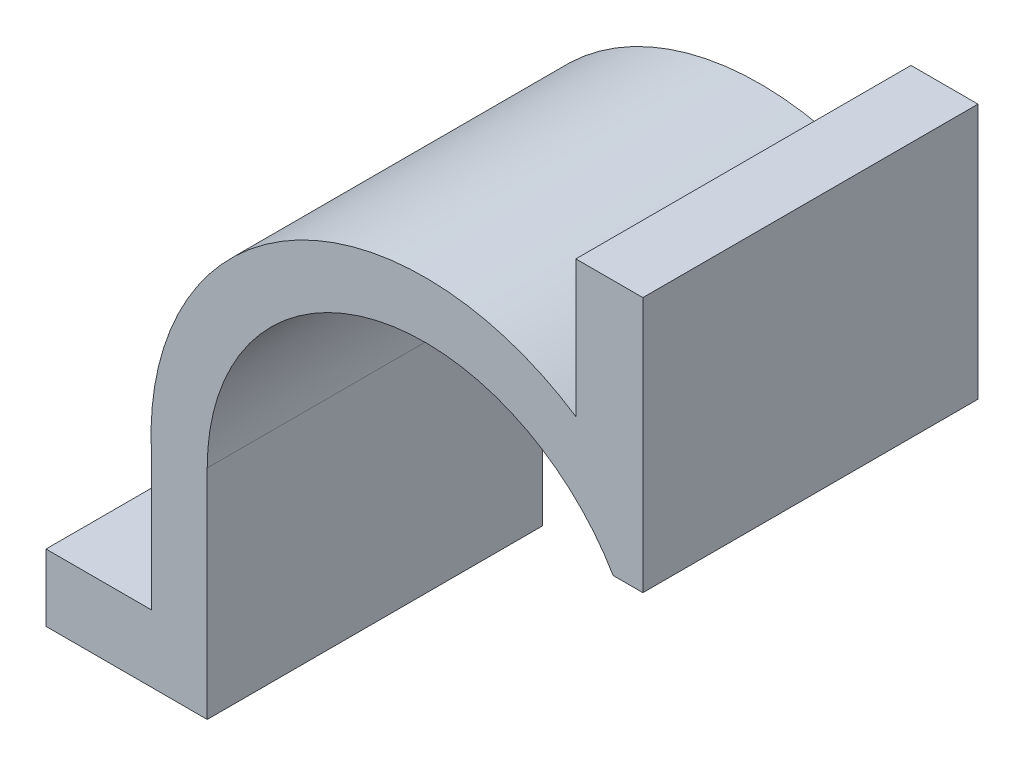
SolidWorks part; units mm, degrees
ref_plane "Front Plane" through (0, 0, 0) normal (0, 0, 1) x (1, 0, 0)
ref_plane "Top Plane" through (0, 0, 0) normal (0, 1, 0) x (1, 0, 0)
ref_plane "Right Plane" through (0, 0, 0) normal (1, 0, 0) x (0, 0, -1)
sketch "Sketch2" plane through (0, 0, 0) normal (0, 0, 1) x (1, 0, 0)
  line L0 (32.5, 0) -> (0, 0) construction
  line L1 (32.5, 0) -> (32.5, 54.5133) construction
  line L2 (43.1161, -32.5) -> (-56.5532, -32.5) construction
  line L3 (0, 32.5) -> (39.8302, 32.5) construction
  line L4 (-32.5, 0) -> (-32.5, -32.5)
  line L5 (-32.5, -31.4301) -> (-32.5, 0) construction
  line L6 (-32.5, -32.5) -> (-56.5532, -32.5)
  line L7 (-56.5532, -32.5) -> (-56.5532, -22.5)
  line L8 (-56.5532, -22.5) -> (-40.8374, -22.5)
  line L9 (-40.8374, -22.5) -> (-40.8374, -2.0108)
  line L10 (28.0694, 16.3817) -> (32.5, 16.3817)
  line L11 (32.5, 16.3817) -> (32.5, 54.5133)
  line L12 (32.5, 54.5133) -> (22.5, 54.5133)
  line L13 (22.5, 54.5133) -> (22.5, 34.1392)
  circle A0 centre (0, 0) radius 31.88 construction
  circle A1 centre (0, 0) radius 32.5 construction
  arc A2 (-32.5, 0) -> (28.0694, 16.3817) centre (0, 0) cw
  arc A3 (-40.8374, -2.0108) -> (22.5, 34.1392) centre (0, 0) cw
  point P22 (0, 0)
extrude "Boss-Extrude1" add sketch "Sketch2" against normal blind 50
